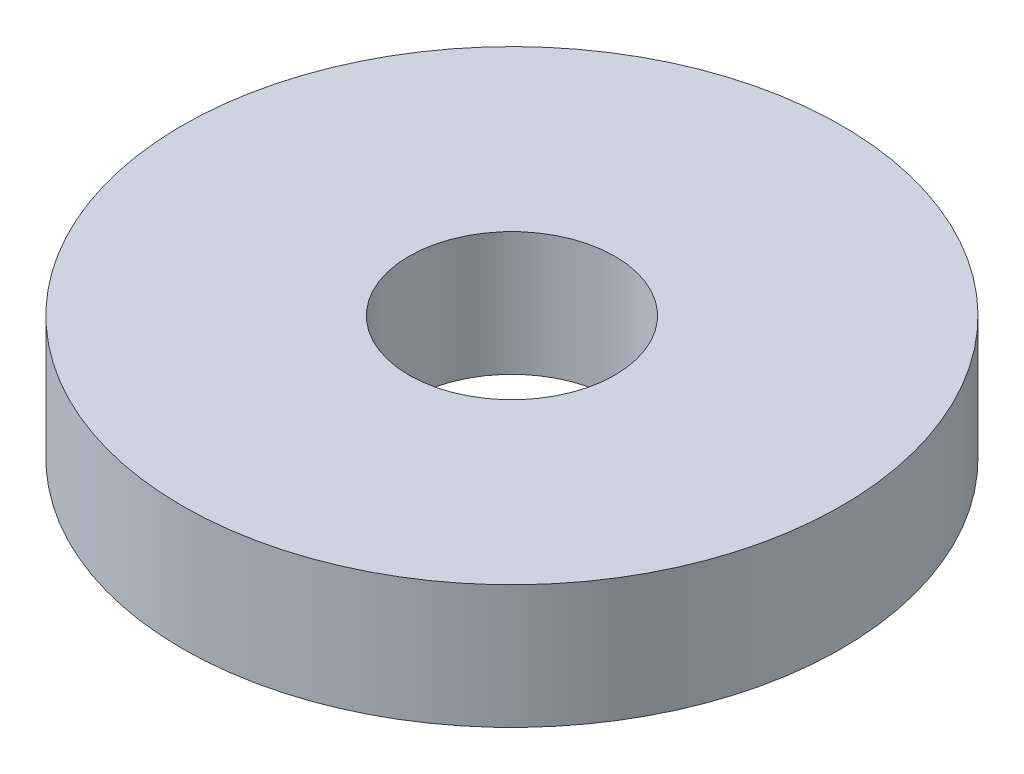
SolidWorks part; units mm, degrees
ref_plane "Front Plane" through (0, 0, 0) normal (0, 0, 1) x (1, 0, 0)
ref_plane "Top Plane" through (0, 0, 0) normal (0, 1, 0) x (1, 0, 0)
ref_plane "Right Plane" through (0, 0, 0) normal (1, 0, 0) x (0, 0, -1)
sketch "Sketch1" plane through (0, 0, 0) normal (0, 1, 0) x (1, 0, 0)
  circle A0 centre (0, 0) radius 10.16
  circle A1 centre (0, 0) radius 3.175
  dimension "D1" = 20.32
  dimension "D2" = 6.35
extrude "Boss-Extrude1" add sketch "Sketch1" along normal blind 3.81
